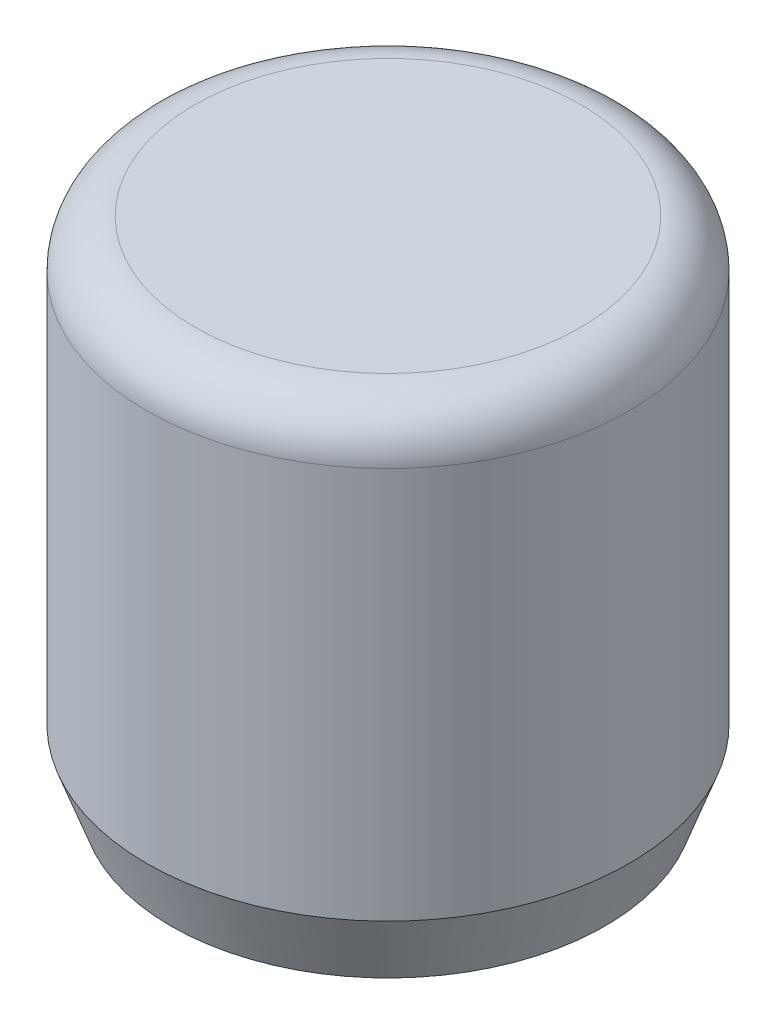
SolidWorks part; units mm, degrees
ref_plane "Спереди" through (0, 0, 0) normal (0, 0, 1) x (1, 0, 0)
ref_plane "Сверху" through (0, 0, 0) normal (0, 1, 0) x (1, 0, 0)
ref_plane "Справа" through (0, 0, 0) normal (1, 0, 0) x (0, 0, -1)
sketch "Sketch1" plane through (0, 0, 0) normal (0, 1, 0) x (1, 0, 0)
  circle A0 centre (0, 0) radius 5
  dimension "D1" = 10
extrude "Boss-Extrude1" add sketch "Sketch1" along normal blind 10.5
sketch "Sketch2" plane through (0, 0, 0) normal (0, -1, 0) x (1, 0, 0)
  circle A0 centre (0, 0) radius 3
  dimension "D1" = 6
extrude "Cut-Extrude1" cut sketch "Sketch2" against normal blind 6
fillet "Fillet1" radius 1 1 edges at (0, 10.5, 5)
chamfer "Chamfer1" distance 0.5 angle 70 1 edges at (0, 0, 5)
